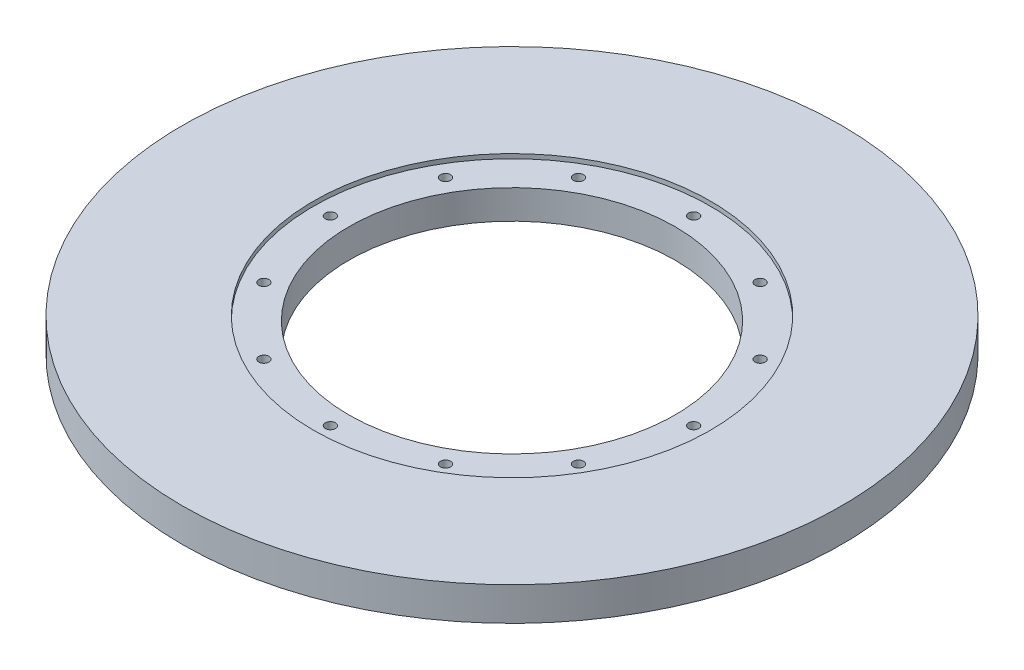
SolidWorks part; units mm, degrees
material "6061-T6 (SS)"
ref_plane "Front Plane" through (0, 0, 0) normal (0, 0, 1) x (1, 0, 0)
ref_plane "Top Plane" through (0, 0, 0) normal (0, 1, 0) x (1, 0, 0)
ref_plane "Right Plane" through (0, 0, 0) normal (1, 0, 0) x (0, 0, -1)
sketch "Sketch1" plane through (0, 0, 0) normal (0, 1, 0) x (1, 0, 0)
  line L5 (0, 0) -> (127.635, 0)
  line L6 (0, 0) -> (0, 127.635)
  line L7 (0, 127.635) -> (127.635, 127.635)
  line L8 (127.635, 0) -> (127.635, 127.635)
  dimension "D1" = 127.635
  dimension "D2" = 127.635
extrude "Boss-Extrude1" add sketch "Sketch1" along normal blind 9.525 contours L5 L8 L7 L6
sketch "Sketch13" plane through (0, 9.525, 0) normal (0, 1, 0) x (1, 0, 0)
  circle A0 centre (63.8175, 63.8175) radius 93.6625
  dimension "D1" = 187.325
extrude "Boss-Extrude2" add sketch "Sketch13" against normal up to surface (9.525 mm away) contours A0 up to face at (63.8175, 0, -63.8175)
sketch "Sketch6" plane through (127.635, 0, 0) normal (1, 0, 0) x (0, 0, -1)
  circle A0 centre (4.7625, 4.7625) radius 1.3526
  dimension "D1" = 2.7051
extrude "6-32 hole1" cut sketch "Sketch6" against normal blind 12.7
sketch "Sketch7" [suppressed] plane through (0, 0, -127.635) normal (0, 0, -1) x (-1, 0, 0)
  circle A0 centre (-122.8725, 4.7625) radius 1.3525
  dimension "D1" = 2.7051
sketch "Sketch8" [suppressed] plane through (0, 0, 0) normal (-1, 0, 0) x (0, 0, 1)
  circle A0 centre (-122.8725, 4.7625) radius 1.3525
  dimension "D1" = 2.7051
sketch "Sketch9" [suppressed] plane through (0, 0, 0) normal (0, 0, 1) x (1, 0, 0)
  circle A0 centre (4.7625, 4.7625) radius 1.3526
  dimension "D1" = 2.7051
sketch "Sketch5" plane through (0, 9.525, 0) normal (0, 1, 0) x (1, 0, 0)
  circle A0 centre (63.8175, 63.8175) radius 46.355
  circle A1 centre (63.8175, 63.8175) radius 93.6625 construction
  dimension "D1" = 92.71
extrude "Cut-Extrude1" cut sketch "Sketch5" against normal blind 9.525
sketch "Sketch11" plane through (0, 9.525, 0) normal (0, 1, 0) x (1, 0, 0)
  line L0 (63.8175, 63.8175) -> (63.8175, 115.443) construction
  circle A0 centre (63.8175, 115.443) radius 1.4351
  dimension "D2" = 2.8702
  dimension "D1" = 51.6255
extrude "Cut-Extrude3" cut sketch "Sketch11" against normal through all contours A0
pattern_circular "CirPattern1" count 12 over 360 about axis through (63.8175, 0, -63.8175) along (0, 1, 0) of "Cut-Extrude3"
sketch "Sketch12" plane through (0, 9.525, 0) normal (0, 1, 0) x (1, 0, 0)
  circle A0 centre (63.8175, 63.8175) radius 56.4198
  dimension "D1" = 112.8395
extrude "Cut-Extrude4" cut sketch "Sketch12" against normal blind 1.27
